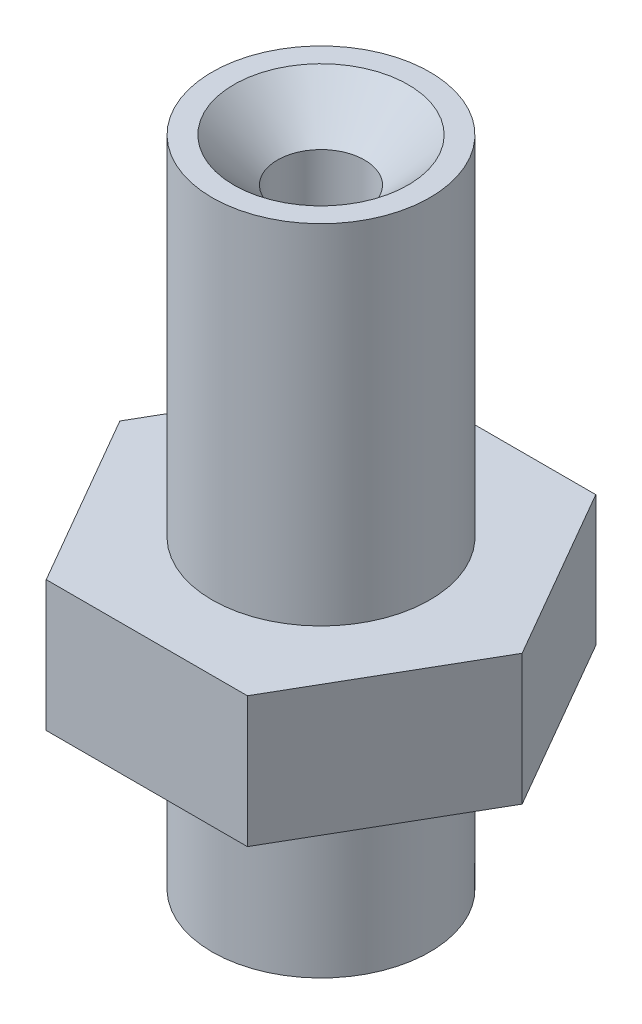
SolidWorks part; units mm, degrees
ref_plane "Front Plane" through (0, 0, 0) normal (0, 0, 1) x (1, 0, 0)
ref_plane "Top Plane" through (0, 0, 0) normal (0, 1, 0) x (1, 0, 0)
ref_plane "Right Plane" through (0, 0, 0) normal (1, 0, 0) x (0, 0, -1)
sketch "Sketch1" plane through (0, 0, 0) normal (0, 1, 0) x (1, 0, 0)
  line L1 (2.3094, 4) -> (-2.3094, 4)
  line L2 (-2.3094, 4) -> (-4.6188, 0)
  line L3 (-4.6188, 0) -> (-2.3094, -4)
  line L4 (-2.3094, -4) -> (2.3094, -4)
  line L5 (2.3094, -4) -> (4.6188, 0)
  line L6 (4.6188, 0) -> (2.3094, 4)
  circle A0 centre (0, 0) radius 4 construction
  dimension "D1" = 8
extrude "Boss-Extrude1" add sketch "Sketch1" along normal mid plane 3
sketch "Sketch4" plane through (0, -1.5, 0) normal (0, -1, 0) x (1, 0, 0)
  circle A0 centre (0, 0) radius 2.5
  dimension "D1" = 5
extrude "Boss-Extrude3" add sketch "Sketch4" along normal blind 4
cosmetic thread "Cosmetic Thread3" parameters "D2"=4.11
sketch "Sketch2" plane through (0, 1.5, 0) normal (0, 1, 0) x (1, 0, 0)
  circle A0 centre (0, 0) radius 2.5
  dimension "D1" = 5
extrude "Boss-Extrude2" add sketch "Sketch2" along normal blind 8
cosmetic thread "Cosmetic Thread2" parameters "D2"=4.11
sketch "Sketch3" plane through (0, 9.5, 0) normal (0, 1, 0) x (1, 0, 0)
  circle A0 centre (0, 0) radius 1
  dimension "D1" = 2
extrude "Cut-Extrude1" cut sketch "Sketch3" against normal through all
chamfer "Chamfer2" distance 1 angle 45 2 edges at (0, 9.5, 1) (0, -5.5, 1)
